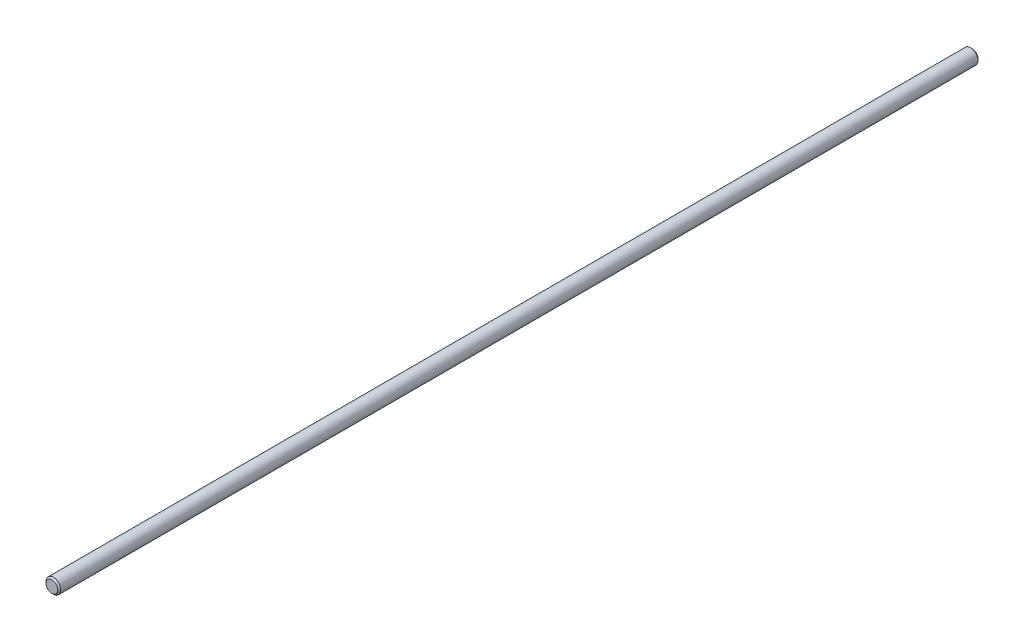
SolidWorks part; units mm, degrees
ref_plane "Front" through (0, 0, 0) normal (0, 0, 1) x (1, 0, 0)
ref_plane "Top" through (0, 0, 0) normal (0, 1, 0) x (1, 0, 0)
ref_plane "Right" through (0, 0, 0) normal (1, 0, 0) x (0, 0, -1)
sketch "Sketch1" plane through (0, 0, 0) normal (0, 0, 1) x (1, 0, 0)
  circle A0 centre (0, 0) radius 8
  dimension "D1" = 16
extrude "Extrude1" add sketch "Sketch1" along normal mid plane 1000
chamfer "Chamfer1" distance 1.6 angle 45 2 edges at (8, 0, -500) (8, 0, 500)
equation "\"D1@Chamfer1\" = \"D1@Sketch1\" * .1"
